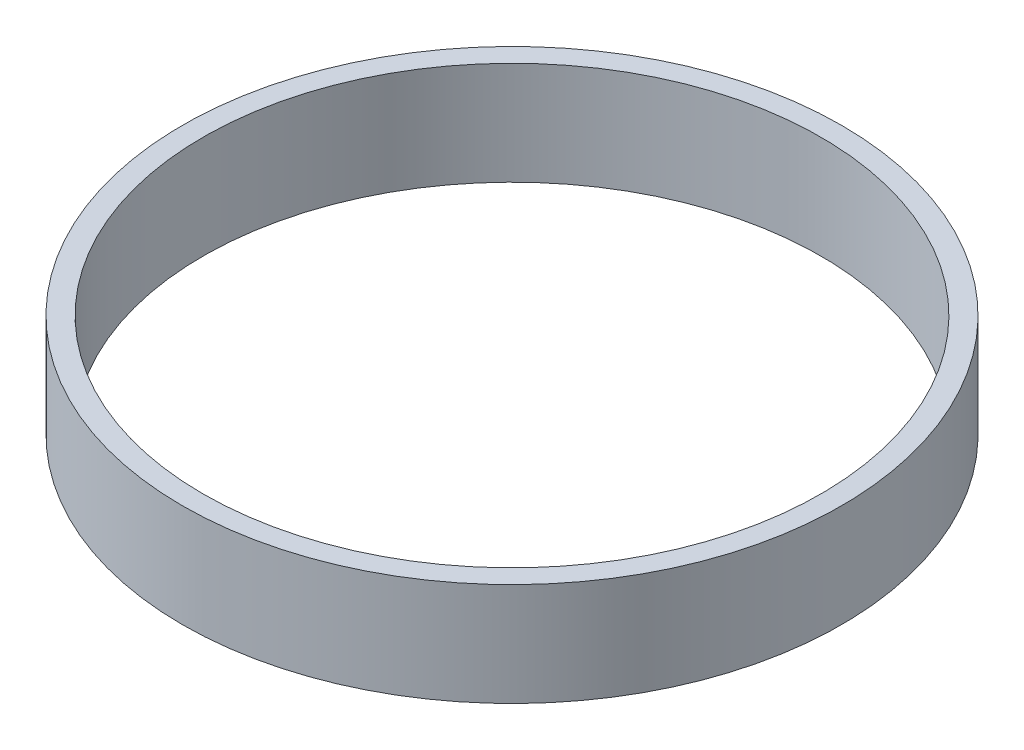
SolidWorks part; units mm, degrees
ref_plane "Front Plane" through (0, 0, 0) normal (0, 0, 1) x (1, 0, 0)
ref_plane "Top Plane" through (0, 0, 0) normal (0, 1, 0) x (1, 0, 0)
ref_plane "Right Plane" through (0, 0, 0) normal (1, 0, 0) x (0, 0, -1)
sketch "Sketch1" plane through (0, 0, 0) normal (0, 1, 0) x (1, 0, 0)
  circle A0 centre (0, 0) radius 30
  circle A1 centre (0, 0) radius 32
  dimension "D1" = 60
  dimension "D2" = 64
extrude "Boss-Extrude1" add sketch "Sketch1" along normal blind 10
